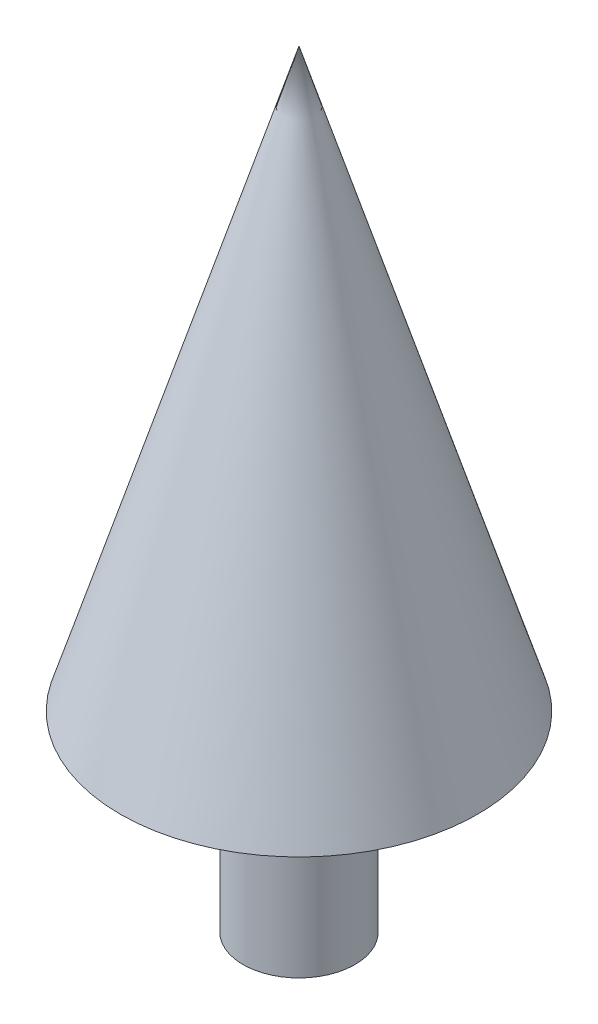
SolidWorks part; units mm, degrees
ref_plane "Front Plane" through (0, 0, 0) normal (0, 0, 1) x (1, 0, 0)
ref_plane "Top Plane" through (0, 0, 0) normal (0, 1, 0) x (1, 0, 0)
ref_plane "Right Plane" through (0, 0, 0) normal (1, 0, 0) x (0, 0, -1)
sketch "Sketch2" plane through (0, 0, 0) normal (0, 0, 1) x (1, 0, 0)
  line L0 (0, 0) -> (0, 450)
  line L1 (0, 450) -> (104.7921, 112.3257)
  line L2 (104.7921, 112.3257) -> (32.8221, 112.3257)
  line L3 (32.8221, 112.3257) -> (32.8221, 0)
  line L4 (32.8221, 0) -> (0, 0)
  point P3 (207.2436, 167.3616)
  point P7 (104.7921, 112.3257)
  dimension "D1" = 450
  dimension "D2" = 112.3257
  dimension "D3" = 32.8221
revolve "Revolve1" add sketch "Sketch2" angle 360 about L0
